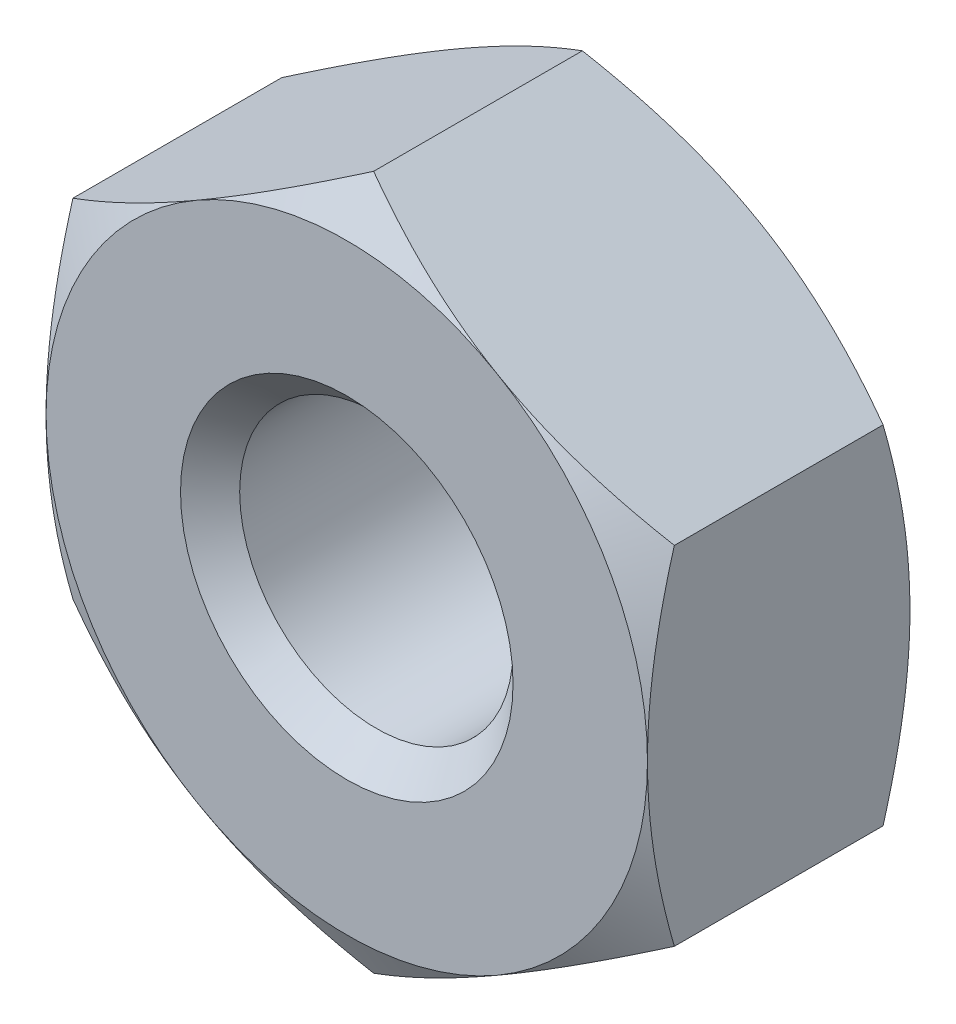
SolidWorks part; units mm, degrees
material "Plain Carbon Steel"
ref_plane "Front Plane" through (0, 0, 0) normal (0, 0, 1) x (1, 0, 0)
ref_plane "Top Plane" through (0, 0, 0) normal (0, 1, 0) x (1, 0, 0)
ref_plane "Right Plane" through (0, 0, 0) normal (1, 0, 0) x (0, 0, -1)
sketch "Sketch2" plane through (0, 0, 0) normal (0, 0, 1) x (1, 0, 0)
  line L0 (2.75, 1.5877) -> (2.75, -1.5877)
  line L1 (-2.75, 1.5877) -> (-2.75, -1.5877)
  line L2 (2.75, 1.5877) -> (0, 3.1754)
  line L3 (0, 3.1754) -> (-2.75, 1.5877)
  line L4 (-2.75, -1.5877) -> (0, -3.1754)
  line L5 (0, -3.1754) -> (2.75, -1.5877)
  circle A0 centre (0, 0) radius 1.25
  dimension "D3" = 2.5
  dimension "D1" = 5.5
  dimension "D2" = 120
  dimension "D4" = 2.75
extrude "Boss-Extrude1" add sketch "Sketch2" along normal mid plane 2.4
sketch "Sketch3" plane through (0, 0, -1.2) normal (0, 0, -1) x (-1, 0, 0)
  line L0 (0, 3.1754) -> (2.75, 1.5877) construction
  line L1 (-2.75, 1.5877) -> (0, 3.1754) construction
  line L2 (-2.75, 1.5877) -> (-2.75, -1.5877) construction
  line L3 (0, -3.1754) -> (-2.75, -1.5877) construction
  line L4 (2.75, -1.5877) -> (0, -3.1754) construction
  line L5 (2.75, 1.5877) -> (2.75, -1.5877) construction
  line L6 (0, 3.1754) -> (2.75, 1.5877) construction
  line L7 (-2.75, 1.5877) -> (0, 3.1754) construction
  line L8 (-2.75, 1.5877) -> (-2.75, -1.5877) construction
  line L9 (0, -3.1754) -> (-2.75, -1.5877) construction
  line L10 (2.75, -1.5877) -> (0, -3.1754) construction
  line L11 (2.75, 1.5877) -> (2.75, -1.5877) construction
  circle A0 centre (0, 0) radius 2.75 construction
sketch "Sketch4" plane through (0, 0, 0) normal (1, 0, 0) x (0, 0, -1)
  line L0 (1.2, -2.75) -> (1.2, 2.75) construction
  line L1 (1.2, -2.75) -> (1.2, 2.75) construction
  line L2 (1.2, 2.75) -> (1.2, 4.3287)
  line L3 (1.2, 4.3287) -> (0.2886, 4.3287)
  line L4 (0.2886, 4.3287) -> (1.2, 2.75)
  line L6 (-2.9945, 0) -> (4.4636, 0) construction
  dimension "D1" = 30
revolve "Cut-Revolve2" cut sketch "Sketch4" angle 360 about L6
mirror "Mirror1" about plane through (0, 0, 0) normal (0, 0, 1) of "Cut-Revolve2"
chamfer "Chamfer1" distance 0.2705 angle 45 2 edges at (1.25, 0, -1.2) (1.25, 0, 1.2)
